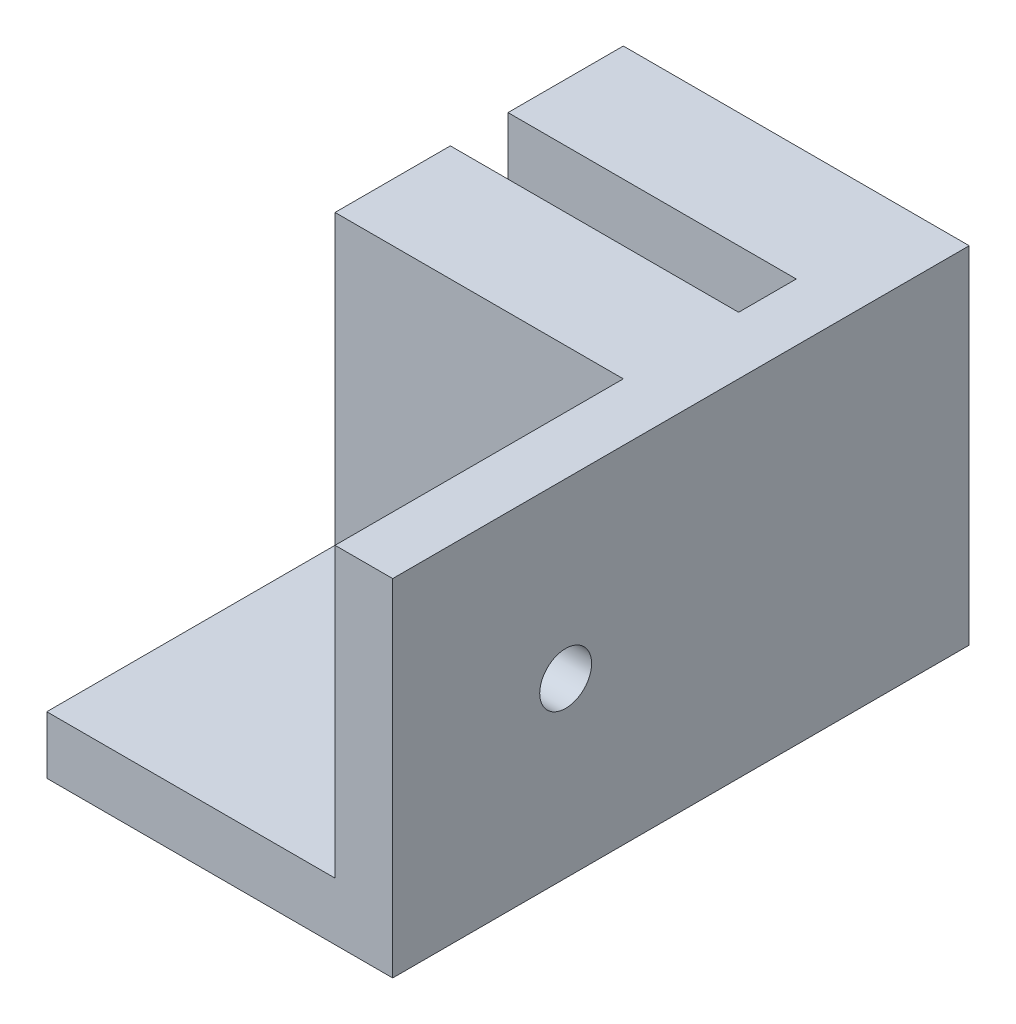
SolidWorks part; units mm, degrees
material "ABS"
ref_plane "Plano frontal" through (0, 0, 0) normal (0, 0, 1) x (1, 0, 0)
ref_plane "Plano superior" through (0, 0, 0) normal (0, 1, 0) x (1, 0, 0)
ref_plane "Plano direito" through (0, 0, 0) normal (1, 0, 0) x (0, 0, -1)
sketch "Esboço1" plane through (0, 0, 0) normal (0, 0, 1) x (1, 0, 0)
  line L9 (0, 0) -> (-30, 0)
  line L10 (0, 0) -> (0, 30)
  line L11 (0, 30) -> (-30, 30)
  line L12 (-30, 0) -> (-30, 30)
  dimension "D1" = 30
  dimension "D2" = 30
extrude "Ressalto-extrusão1" add sketch "Esboço1" along normal blind 50
sketch "Esboço2" plane through (0, 30, 0) normal (0, 1, 0) x (1, 0, 0)
  line L0 (-30, -50) -> (-30, 0) construction
  line L1 (-30, -10) -> (-5, -10)
  line L2 (-30, -10) -> (-30, -15)
  line L3 (-30, -15) -> (-5, -15)
  line L4 (-5, -10) -> (-5, -15)
  line L5 (0, 0) -> (-30, 0) construction
  line L6 (0, -50) -> (0, 0) construction
  dimension "D1" = 10
  dimension "D2" = 5
  dimension "D3" = 5
extrude "Corte-extrusão1" cut sketch "Esboço2" against normal through all
sketch "Esboço3" plane through (0, 30, 0) normal (0, 1, 0) x (1, 0, 0)
  line L0 (0, -50) -> (0, 0) construction
  line L1 (-5, -25) -> (-30, -25)
  line L2 (-5, -25) -> (-5, -50)
  line L3 (-5, -50) -> (-30, -50)
  line L4 (-30, -25) -> (-30, -50)
  line L5 (-30, -15) -> (-5, -15) construction
  dimension "D1" = 5
  dimension "D2" = 10
extrude "Corte-extrusão2" cut sketch "Esboço3" against normal blind 25
hole_wizard "Furo com folga de M41" positions "3DSketch1" profile "Esboço4" hole size "M4" standard "ISO" end condition through all
sketch3d "3DSketch1"
  line L0 (-5, 5, 25) -> (-30, 5, 25) construction
  line L1 (-5, 5, 25) -> (-5, 30, 25) construction
  line L2 (-5, 5, 50) -> (-5, 5, 25) construction
  point P0 (-15, 5, 35)
  point P2 (-5, 15, 35)
  dimension "D1" = 10
  dimension "D4" = 10
  dimension "D5" = 10
  dimension "D6" = 10
sketch "Esboço4" plane through (-15, 5, 35) normal (1, 0, 0) x (0, 0, 1)
  line L0 (0, 0) -> (0, 5)
  line L1 (0, 5) -> (2.25, 5)
  line L2 (2.25, 5) -> (2.25, 0)
  line L5 (2.25, 0) -> (0, 0)
  line L11 (0, -6.35) -> (0, 107.95) construction
  dimension "Thru Hole Dia." = 4.5
  dimension "Thru Hole Depth" = 5
